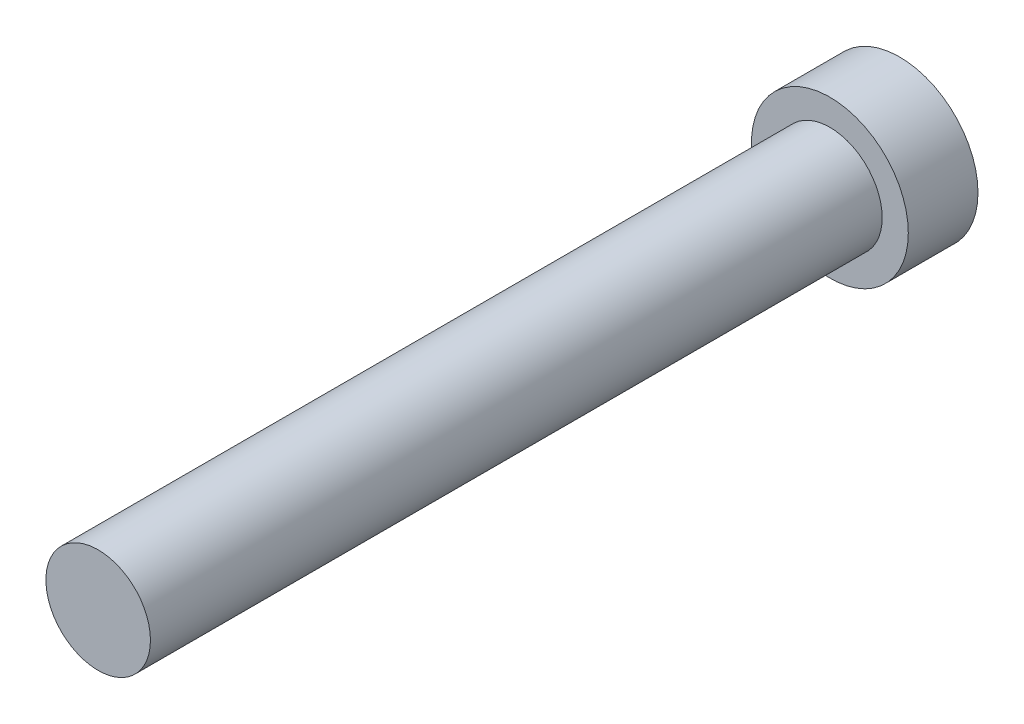
SolidWorks part; units mm, degrees
ref_plane "Front Plane" through (0, 0, 0) normal (0, 0, 1) x (1, 0, 0)
ref_plane "Top Plane" through (0, 0, 0) normal (0, 1, 0) x (1, 0, 0)
ref_plane "Right Plane" through (0, 0, 0) normal (1, 0, 0) x (0, 0, -1)
sketch "Sketch1" plane through (0, 0, 0) normal (0, 0, 1) x (1, 0, 0)
  circle A0 centre (-36.5589, 15.1419) radius 22.5
  dimension "D1" = 45
extrude "Boss-Extrude1" add sketch "Sketch1" along normal blind 20
sketch "Sketch2" plane through (0, 0, 20) normal (0, 0, 1) x (1, 0, 0)
  circle A0 centre (-36.5589, 15.1419) radius 15
  dimension "D1" = 30
extrude "Boss-Extrude2" add sketch "Sketch2" along normal blind 210
